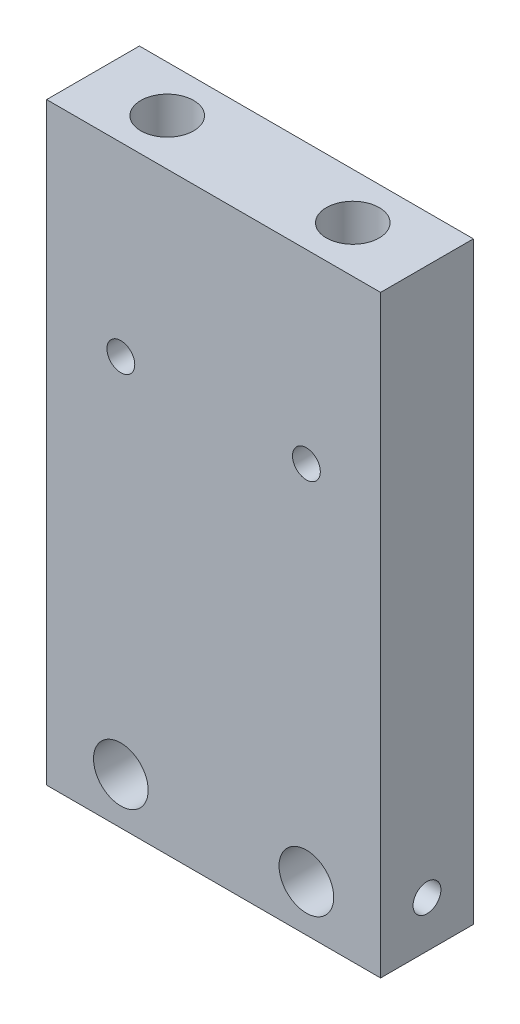
SolidWorks part; units mm, degrees
material "6061-T6 (SS)"
ref_plane "Front" through (0, 0, 0) normal (0, 0, 1) x (1, 0, 0)
ref_plane "Top" through (0, 0, 0) normal (0, 1, 0) x (1, 0, 0)
ref_plane "Right" through (0, 0, 0) normal (1, 0, 0) x (0, 0, -1)
sketch "Sketch1" plane through (0, 0, 0) normal (0, 0, 1) x (1, 0, 0)
  line L1 (0, 0) -> (-18, 0)
  line L2 (0, 0) -> (0, 32)
  line L3 (0, 32) -> (-18, 32)
  line L4 (-18, 0) -> (-18, 32)
  dimension "D1" = 18
  dimension "D2" = 32
extrude "Extrude1" add sketch "Sketch1" along normal blind 5
ref_plane "Plane1" through (-9, 0, 0) normal (1, 0, 0) x (0, 0, -1)
hole_wizard "#4-40 Tapped Hole1" positions "3DSketch1" profile "Sketch2" tap size "#4-40" standard "Ansi Inch"
sketch3d "3DSketch1"
  line L0 (0, 32, 5) -> (-18, 32, 5) construction
  point P0 (-14, 32, 2.5)
  dimension "D1" = 2.5
  dimension "D2" = 5
sketch "Sketch2" plane through (-14, 32, 2.5) normal (1, 0, 0) x (0, 0, 1)
  line L0 (0, 0) -> (0, 10.8138)
  line L1 (0, 10.8138) -> (1.1303, 10.1346)
  line L2 (1.1303, 10.1346) -> (1.1303, 8.2296)
  line L3 (1.1303, 8.2296) -> (1.4224, 8.2296)
  line L4 (1.4224, 8.2296) -> (1.4224, 0)
  line L5 (1.4224, 0) -> (0, 0)
  line L10 (0, 10.8138) -> (-1.1303, 10.1346) construction
  line L11 (0, -6.35) -> (0, 107.95) construction
  dimension "Tap Drill Dia." = 2.2606
  dimension "Tap Drill Depth" = 10.1346
  dimension "Thread Major Dia." = 2.8448
  dimension "Thread Depth" = 8.2296
  dimension "Drill Angle" = 118
sketch "Sketch3" plane through (0, 0, 5) normal (0, 0, 1) x (1, 0, 0)
  line L0 (-9, -2.75) -> (-9, 2.75) construction
  line L1 (-18, 0) -> (0, 0) construction
  line L2 (0, 32) -> (-18, 32) construction
  circle A0 centre (-14, 22) radius 0.75
  circle A1 centre (-14, 2.5) radius 1.4732
  dimension "D4" = 1.5
  dimension "D5" = 2.9464
  dimension "D1" = 5
  dimension "D2" = 2.5
  dimension "D3" = 10
extrude "Extrude2" cut sketch "Sketch3" against normal through all
sketch "Sketch4" plane through (-18, 0, 0) normal (-1, 0, 0) x (0, 0, 1)
  line L0 (5, 0) -> (0, 0) construction
  line L1 (5, 32) -> (5, 0) construction
  circle A0 centre (2.5, 2.5) radius 0.75
  dimension "D2" = 1.5
  dimension "D1" = 2.5
  dimension "D3" = 2.5
extrude "Extrude3" cut sketch "Sketch4" against normal blind 2.794
mirror "Mirror2" about plane through (-9, 0, 0) normal (1, 0, 0) of "Extrude3", "Extrude2", "#4-40 Tapped Hole1"
